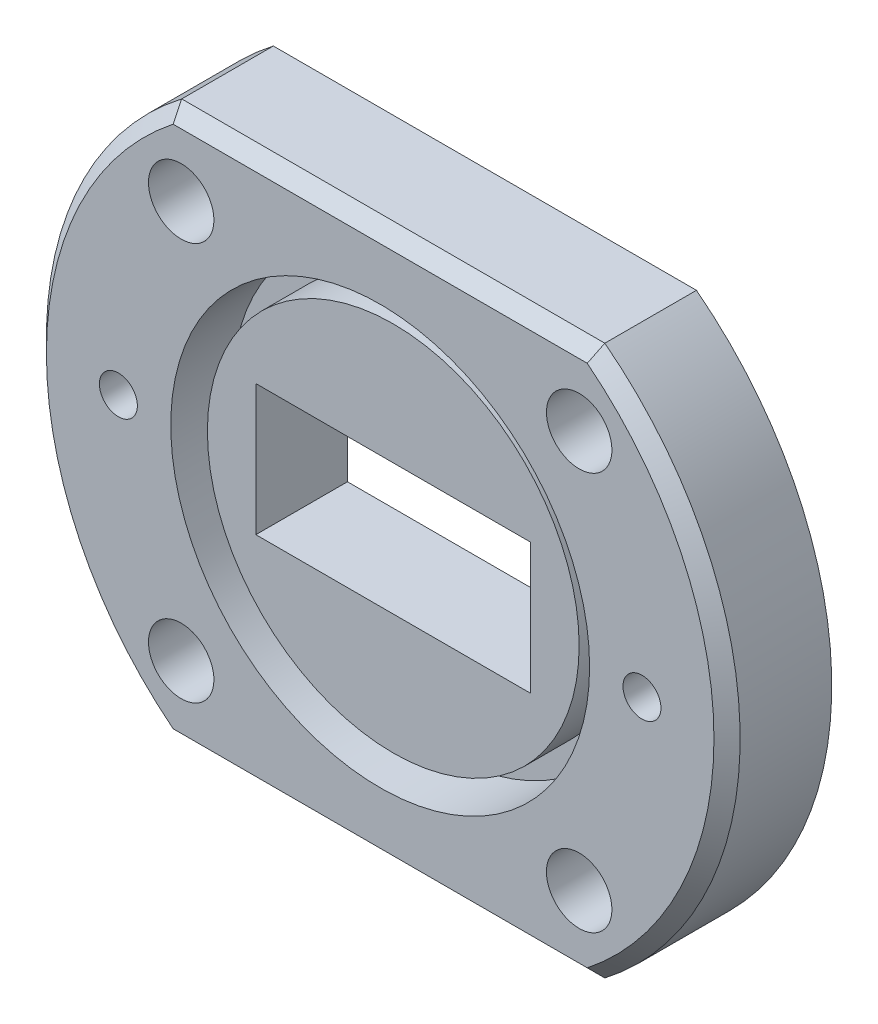
SolidWorks part; units mm, degrees
material "Латунь"
ref_plane "Спереди" through (0, 0, 0) normal (0, 0, 1) x (1, 0, 0)
ref_plane "Сверху" through (0, 0, 0) normal (0, 1, 0) x (1, 0, 0)
ref_plane "Справа" through (0, 0, 0) normal (1, 0, 0) x (0, 0, -1)
sketch "Эскиз1" plane through (0, 0, 0) normal (0, 0, 1) x (1, 0, 0)
  circle A0 centre (0, 0) radius 26.5
  dimension "D1" = 53
extrude "Бобышка-Вытянуть1" add sketch "Эскиз1" along normal blind 8
sketch "Эскиз2" plane through (0, 0, 8) normal (0, 0, 1) x (1, 0, 0)
  circle A0 centre (0, 0) radius 16
  circle A1 centre (0, 0) radius 26.5 construction
  dimension "D1" = 10.5
extrude "Вырез-Вытянуть1" cut sketch "Эскиз2" against normal blind 1
sketch "Эскиз3" plane through (0, 0, 7) normal (0, 0, 1) x (1, 0, 0)
  circle A0 centre (0, 0) radius 16 construction
  circle A1 centre (0, 0) radius 16
  circle A2 centre (0, 0) radius 14.2
  dimension "D1" = 1.8
extrude "Вырез-Вытянуть2" cut sketch "Эскиз3" against normal blind 3.7
sketch "Эскиз4" plane through (0, 0, 7) normal (0, 0, 1) x (1, 0, 0)
  line L1 (-10.5, -5) -> (10.5, -5)
  line L2 (-10.5, -5) -> (-10.5, 5)
  line L3 (-10.5, 5) -> (10.5, 5)
  line L4 (10.5, -5) -> (10.5, 5)
  line L5 (-10.5, -5) -> (10.5, 5) construction
  line L6 (-10.5, 5) -> (10.5, -5) construction
  point P0 (0, 0)
  dimension "D1" = 10
  dimension "D2" = 21
extrude "Вырез-Вытянуть3" cut sketch "Эскиз4" against normal through all
sketch "Эскиз5" plane through (0, 0, 8) normal (0, 0, 1) x (1, 0, 0)
  line L0 (-15.2028, 15.2028) -> (0, 0) construction
  line L1 (0, 0) -> (-21.5, 0) construction
  circle A0 centre (0, 0) radius 21.5 construction
  circle A1 centre (-15.2028, 15.2028) radius 2.5
  dimension "D1" = 43
  dimension "D2" = 5
  dimension "D3" = 45
extrude "Вырез-Вытянуть4" cut sketch "Эскиз5" against normal through all
pattern_circular "Круговой массив1" count 4 over 360 about axis through (0, 0, 0) along (0, 0, 1) of "Вырез-Вытянуть4"
chamfer "Фаска1" distance 1 angle 45 1 edges at (26.5, 0, 8)
sketch "Эскиз6" plane through (0, 0, 0) normal (0, 0, 1) x (1, 0, 0)
  line L0 (0, 0) -> (0, 32.6635) construction
  line L2 (0, 21) -> (30, 21)
  line L3 (0, 21) -> (0, 51)
  line L4 (0, 51) -> (30, 51)
  line L5 (30, 21) -> (30, 51)
  dimension "D1" = 21
  dimension "D2" = 30
revolve "Вырез-Повернуть1" cut sketch "Эскиз6" angle 360 about L0
mirror "Зеркальное отражение1" about plane through (0, 0, 0) normal (0, 1, 0) of "Вырез-Повернуть1"
sketch "Эскиз7" plane through (0, 0, 8) normal (0, 0, 1) x (1, 0, 0)
  point P0 (-20, 0)
  dimension "D1" = 20
hole_wizard "Отверстие обработанное метчиком M3.5x0.61" positions "Трехмерный эскиз1" profile "Эскиз8" tap size "M3.5x0.6" standard "Ansi Metric" end condition through all
sketch3d "Трехмерный эскиз1"
  point P0 (-20, 0, 8)
sketch "Эскиз8" plane through (-20, 0, 8) normal (1, 0, 0) x (0, -1, 0)
  line L0 (0, 0) -> (0, 8)
  line L1 (0, 8) -> (1.45, 8)
  line L2 (1.45, 8) -> (1.45, 0)
  line L5 (1.45, 0) -> (0, 0)
  line L11 (0, -6.35) -> (0, 107.95) construction
  dimension "Диаметр проходного сверла" = 2.9
  dimension "Глубина проходного сверла" = 8
cosmetic thread "Отверстие резьбы1" parameters "D2"=3.5
mirror "Зеркальное отражение2" about plane through (0, 0, 0) normal (1, 0, 0) of "Отверстие обработанное метчиком M3.5x0.61"
chamfer "Фаска2" distance 1 angle 45 2 edges at (0, -21, 8) (0, 21, 8)
